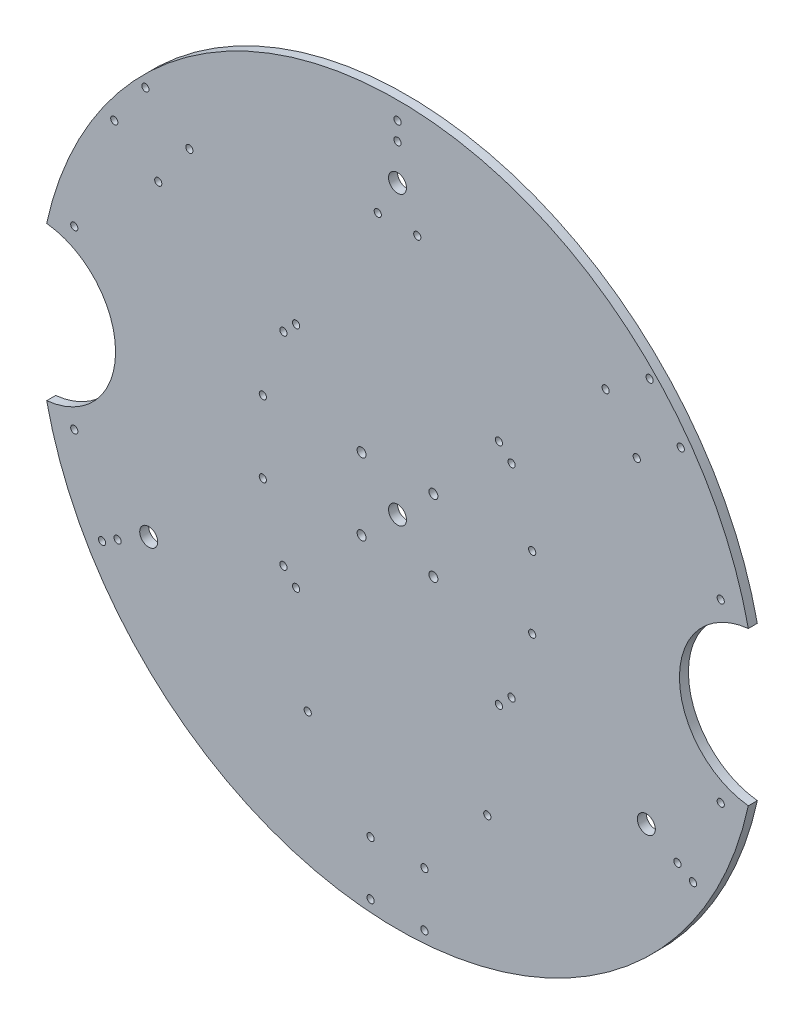
SolidWorks part; units mm, degrees
material "7075-T6 (SN)"
ref_plane "Front Plane" through (0, 0, 0) normal (0, 0, 1) x (1, 0, 0)
ref_plane "Top Plane" through (0, 0, 0) normal (0, 1, 0) x (1, 0, 0)
ref_plane "Right Plane" through (0, 0, 0) normal (1, 0, 0) x (0, 0, -1)
sketch "Sketch1" plane through (0, 0, 0) normal (0, 0, 1) x (1, 0, 0)
  circle A0 centre (0, 0) radius 200
  dimension "D1" = 400
extrude "Boss-Extrude1" add sketch "Sketch1" along normal blind 5
sketch "Sketch3" plane through (0, 0, 5) normal (0, 0, 1) x (1, 0, 0)
  line L0 (0, 0) -> (0, 311.3165) construction
  circle A0 centre (0, 0) radius 185 construction
  circle A6 centre (0, 190) radius 2
  circle A7 centre (0, 180) radius 2
  point P12 (0, 185)
  point P17 (0, 185)
  dimension "D3" = 370
  dimension "D4" = 4
  dimension "D5" = 4
  dimension "D1" = 10
  dimension "D2" = 190
extrude "Cut-Extrude1" cut sketch "Sketch3" against normal up to next (5 mm away)
pattern_circular "CirPattern1" count 3 over 360 about axis through (0, 0, 0) along (0, 0, 1) of "Cut-Extrude1"
sketch "Sketch4" plane through (0, 0, 5) normal (0, 0, 1) x (1, 0, 0)
  line L0 (-258.0607, 0) -> (265.5915, 0) construction
  line L1 (0, -312.9691) -> (0, 312.5871) construction
  circle A0 centre (-200, 0) radius 43
  circle A1 centre (200, 0) radius 43
  circle A2 centre (0, 0) radius 200 construction
  dimension "D1" = 86
  dimension "D2" = 86
  dimension "D3" = 200
  dimension "D4" = 200
extrude "Cut-Extrude2" cut sketch "Sketch4" against normal up to next
sketch "Sketch5" plane through (0, 0, 5) normal (0, 0, 1) x (1, 0, 0)
  circle A0 centre (0, 0) radius 186.5503 construction
  circle A1 centre (180, 49) radius 2
  circle A2 centre (180, -49) radius 2
  circle A3 centre (-180, -49) radius 2
  circle A4 centre (-180, 49) radius 2
  dimension "D1" = 373.1005
extrude "Cut-Extrude3" cut sketch "Sketch5" against normal up to next
sketch "Sketch6" plane through (0, 0, 5) normal (0, 0, 1) x (1, 0, 0)
  line L1 (20, 20) -> (-20, 20) construction
  line L2 (20, 20) -> (20, -20) construction
  line L3 (20, -20) -> (-20, -20) construction
  line L4 (-20, 20) -> (-20, -20) construction
  line L5 (20, 20) -> (-20, -20) construction
  line L6 (20, -20) -> (-20, 20) construction
  circle A0 centre (-20, -20) radius 2.5
  circle A1 centre (-20, 20) radius 2.5
  circle A2 centre (0, 0) radius 5
  circle A3 centre (20, -20) radius 2.5
  circle A4 centre (20, 20) radius 2.5
  point P0 (0, 0)
  dimension "D3" = 5
  dimension "D4" = 5
  dimension "D5" = 5
  dimension "D6" = 5
  dimension "D7" = 10
  dimension "D1" = 40
  dimension "D2" = 40
extrude "Cut-Extrude4" cut sketch "Sketch6" against normal up to next
sketch "Sketch7" plane through (0, 0, 5) normal (0, 0, 1) x (1, 0, 0)
  line L0 (0, 0) -> (0, -215.2075) construction
  line L1 (0, 0) -> (-192.4733, 161.5043) construction
  line L2 (0, 0) -> (211.1351, 177.1634) construction
  line L3 (156.0567, 87.605) -> (117.591, 142.0127) construction
  line L4 (-113.8332, 147.3279) -> (-159.8146, 82.2898) construction
  line L5 (56.2329, -178) -> (-56.2329, -178) construction
  line L6 (0, 0) -> (0, 258.8994) construction
  line L7 (15, -163) -> (-15, -163) construction
  line L8 (15, -163) -> (15, -193) construction
  line L9 (-15, -163) -> (-15, -193) construction
  line L10 (15, -193) -> (-15, -193) construction
  line L11 (15, -163) -> (-15, -193) construction
  line L12 (-15, -163) -> (15, -193) construction
  line L13 (157.7313, 111.2201) -> (140.4127, 135.7163) construction
  line L14 (157.7313, 111.2201) -> (133.2351, 93.9014) construction
  line L15 (140.4127, 135.7163) -> (115.9164, 118.3976) construction
  line L16 (133.2351, 93.9014) -> (115.9164, 118.3976) construction
  line L17 (157.7313, 111.2201) -> (115.9164, 118.3976) construction
  line L18 (140.4127, 135.7163) -> (133.2351, 93.9014) construction
  line L19 (-115.9164, 118.3976) -> (-133.2351, 93.9014) construction
  line L20 (-115.9164, 118.3976) -> (-140.4127, 135.7163) construction
  line L21 (-133.2351, 93.9014) -> (-157.7313, 111.2201) construction
  line L22 (-140.4127, 135.7163) -> (-157.7313, 111.2201) construction
  line L23 (-115.9164, 118.3976) -> (-157.7313, 111.2201) construction
  line L24 (-133.2351, 93.9014) -> (-140.4127, 135.7163) construction
  circle A0 centre (-15, -193) radius 2
  circle A1 centre (15, -193) radius 2
  circle A2 centre (15, -163) radius 2
  circle A3 centre (-15, -163) radius 2
  circle A4 centre (133.2351, 93.9014) radius 2
  circle A5 centre (115.9164, 118.3976) radius 2
  circle A6 centre (140.4127, 135.7163) radius 2
  circle A7 centre (157.7313, 111.2201) radius 2
  circle A8 centre (-157.7313, 111.2201) radius 2
  circle A9 centre (-133.2351, 93.9014) radius 2
  circle A10 centre (-115.9164, 118.3976) radius 2
  circle A11 centre (-140.4127, 135.7163) radius 2
  point P11 (0, -178)
  point P12 (136.8239, 114.8088)
  point P13 (-136.8239, 114.8088)
  point P16 (0, -178)
  point P17 (136.8239, 114.8088)
  point P22 (-136.8239, 114.8088)
  dimension "D14" = 4
  dimension "D15" = 4
  dimension "D16" = 4
  dimension "D17" = 4
  dimension "D18" = 4
  dimension "D19" = 4
  dimension "D20" = 4
  dimension "D21" = 4
  dimension "D22" = 4
  dimension "D23" = 4
  dimension "D24" = 4
  dimension "D25" = 4
  dimension "D1" = 130
  dimension "D2" = 130
  dimension "D3" = 35.26
  dimension "D4" = 35.26
  dimension "D5" = 178
  dimension "D6" = 178
  dimension "D7" = 178
  dimension "D8" = 30
  dimension "D9" = 30
  dimension "D10" = 30
  dimension "D11" = 30
  dimension "D12" = 30
  dimension "D13" = 30
extrude "Cut-Extrude5" cut sketch "Sketch7" against normal up to next
sketch "Sketch8" plane through (0, 0, 5) normal (0, 0, 1) x (1, 0, 0)
  line L0 (0, 0) -> (0, 250.0998) construction
  line L1 (11, 140) -> (-11, 140) construction
  circle A0 centre (-11, 140) radius 2
  circle A1 centre (11, 140) radius 2
  point P5 (0, 140)
  dimension "D3" = 4
  dimension "D4" = 4
  dimension "D1" = 22
  dimension "D2" = 140
extrude "Cut-Extrude6" cut sketch "Sketch8" against normal up to next
sketch "Sketch9" plane through (0, 0, 5) normal (0, 0, 1) x (1, 0, 0)
  line L1 (75, 20) -> (-75, 20) construction
  line L2 (75, 20) -> (75, -20) construction
  line L3 (75, -20) -> (-75, -20) construction
  line L4 (-75, 20) -> (-75, -20) construction
  line L5 (75, 20) -> (-75, -20) construction
  line L6 (75, -20) -> (-75, 20) construction
  circle A0 centre (75, -20) radius 2
  circle A1 centre (75, 20) radius 2
  circle A2 centre (-75, -20) radius 2
  circle A3 centre (-75, 20) radius 2
  point P0 (0, 0)
  dimension "D3" = 4
  dimension "D4" = 4
  dimension "D5" = 4
  dimension "D6" = 4
  dimension "D1" = 150
  dimension "D2" = 40
extrude "Cut-Extrude7" cut sketch "Sketch9" against normal up to next
sketch "Sketch10" plane through (0, 0, 0) normal (0, 0, -1) x (-1, 0, 0)
  line L0 (0, 0) -> (0, 228.857) construction
  line L1 (0, 0) -> (227.9376, -131.5998) construction
  line L2 (0, 0) -> (-251.8595, -145.4112) construction
  circle A0 centre (0, 0) radius 160 construction
  circle A1 centre (-138.5641, -80) radius 5
  circle A2 centre (138.5641, -80) radius 5
  circle A3 centre (0, 160) radius 5
  dimension "D1" = 320
  dimension "D4" = 10
  dimension "D5" = 10
  dimension "D6" = 10
  dimension "D2" = 120
  dimension "D3" = 120
sketch "Sketch11" plane through (0, 0, 0) normal (0, 0, -1) x (-1, 0, 0)
  line L0 (0, 0) -> (0, -191.3116) construction
  line L1 (-50, -120) -> (50, -120) construction
  circle A0 centre (-50, -120) radius 2
  circle A1 centre (50, -120) radius 2
  point P5 (0, -120)
  dimension "D3" = 4
  dimension "D4" = 4
  dimension "D1" = 100
  dimension "D2" = 120
extrude "Cut-Extrude8" cut sketch "Sketch11" against normal up to next
sketch "Sketch12" plane through (0, 0, 0) normal (0, 0, -1) x (-1, 0, 0)
  line L0 (-63.5355, 56.4645) -> (-56.4645, 63.5355) construction
  line L1 (-60, -60) -> (60, -60) construction
  line L2 (-60, -60) -> (-60, 60) construction
  line L3 (-60, 60) -> (60, 60) construction
  line L4 (60, -60) -> (60, 60) construction
  line L5 (-60, -60) -> (60, 60) construction
  line L6 (-60, 60) -> (60, -60) construction
  line L7 (63.5355, 56.4645) -> (56.4645, 63.5355) construction
  line L8 (56.4645, -63.5355) -> (63.5355, -56.4645) construction
  line L9 (-56.4645, -63.5355) -> (-63.5355, -56.4645) construction
  circle A0 centre (-63.5355, -56.4645) radius 2
  circle A1 centre (-56.4645, -63.5355) radius 2
  circle A2 centre (63.5355, -56.4645) radius 2
  circle A3 centre (56.4645, -63.5355) radius 2
  circle A4 centre (63.5355, 56.4645) radius 2
  circle A5 centre (56.4645, 63.5355) radius 2
  circle A6 centre (-56.4645, 63.5355) radius 2
  circle A7 centre (-63.5355, 56.4645) radius 2
  point P0 (0, 0)
  point P14 (-60, 60)
  point P15 (60, 60)
  point P16 (60, -60)
  point P17 (-60, -60)
  dimension "D7" = 4
  dimension "D8" = 4
  dimension "D9" = 4
  dimension "D10" = 4
  dimension "D11" = 4
  dimension "D12" = 4
  dimension "D13" = 4
  dimension "D14" = 4
  dimension "D1" = 120
  dimension "D2" = 120
  dimension "D3" = 10
  dimension "D4" = 10
  dimension "D5" = 10
  dimension "D6" = 10
extrude "Cut-Extrude9" cut sketch "Sketch12" against normal up to next
extrude "Cut-Extrude10" cut sketch "Sketch10" against normal up to next
